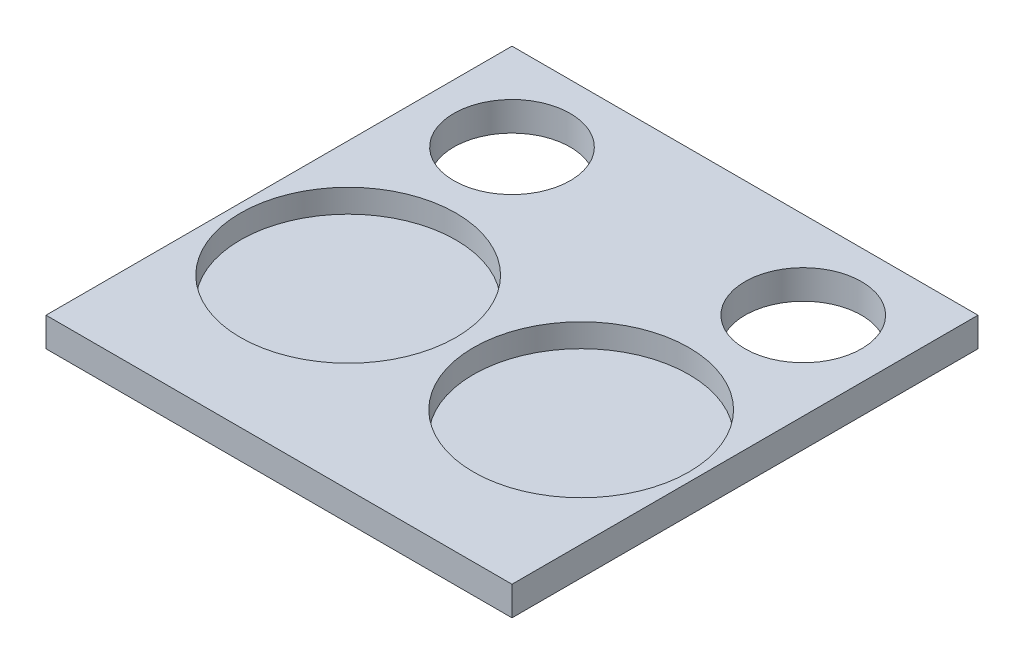
SolidWorks part; units mm, degrees
ref_plane "Front Plane" through (0, 0, 0) normal (0, 0, 1) x (1, 0, 0)
ref_plane "Top Plane" through (0, 0, 0) normal (0, 1, 0) x (1, 0, 0)
ref_plane "Right Plane" through (0, 0, 0) normal (1, 0, 0) x (0, 0, -1)
sketch "Sketch1" plane through (0, 0, 0) normal (0, 1, 0) x (1, 0, 0)
  line L0 (-31.75, 44.45) -> (-31.75, 50.8) construction
  line L1 (-50.8, -50.8) -> (50.8, -50.8)
  line L2 (-50.8, -50.8) -> (-50.8, 50.8)
  line L3 (-50.8, 50.8) -> (50.8, 50.8)
  line L4 (50.8, -50.8) -> (50.8, 50.8)
  line L5 (-50.8, -50.8) -> (50.8, 50.8) construction
  line L6 (-50.8, 50.8) -> (50.8, -50.8) construction
  circle A0 centre (-31.75, 31.75) radius 12.7
  circle A1 centre (31.75, 31.75) radius 12.7
  point P0 (0, 0)
  dimension "D2" = 25.4
  dimension "D1" = 101.6
  dimension "D3" = 6.35
extrude "Boss-Extrude1" add sketch "Sketch1" along normal mid plane 6.35
sketch "Sketch2" plane through (0, 3.175, 0) normal (0, 1, 0) x (1, 0, 0)
  line L0 (-25.4, -10.3185) -> (25.4, -10.3185) construction
  line L1 (0, -10.3185) -> (0, 0) construction
  line L2 (-50.8, 50.8) -> (-50.8, -50.8) construction
  line L3 (29.8545, 19.1923) -> (28.9067, 12.9134) construction
  circle A0 centre (-25.4, -10.3185) radius 23.495
  circle A1 centre (25.4, -10.3185) radius 23.495
  circle A2 centre (31.75, 31.75) radius 12.7 construction
  point P9 (0, -10.3185)
  point P10 (31.75, 31.75)
  dimension "D1" = 46.99
  dimension "D2" = 25.4
  dimension "D3" = 6.35
extrude "Cut-Extrude1" cut sketch "Sketch2" against normal blind 5.08
